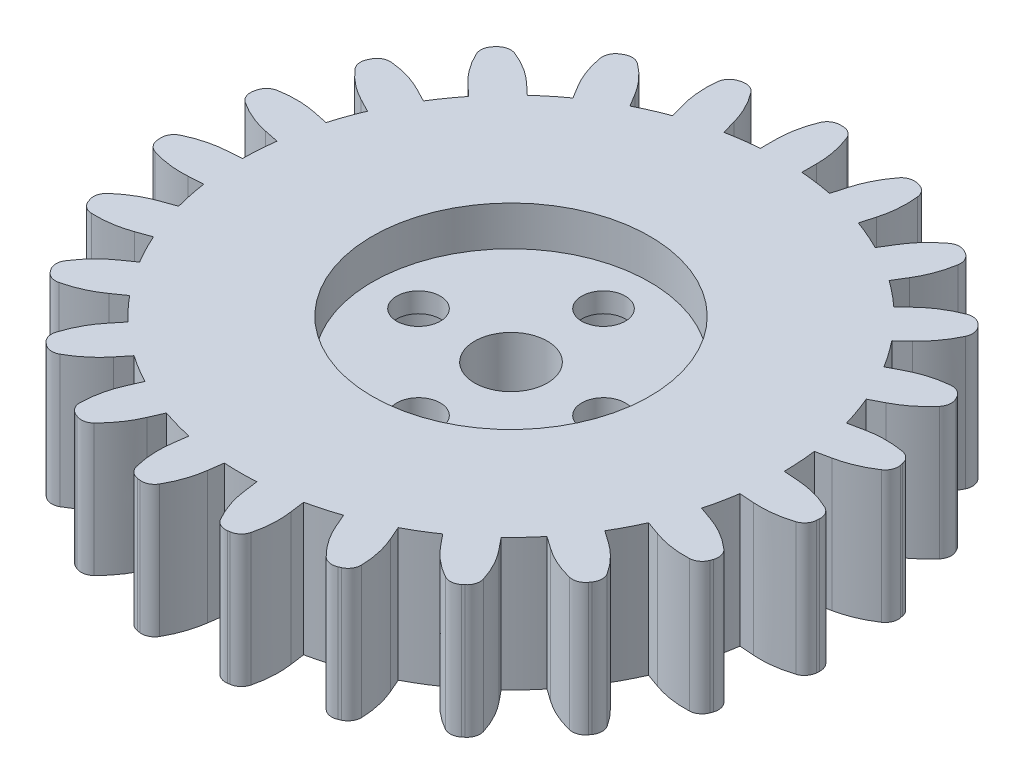
SolidWorks part; units mm, degrees
ref_plane "Plan de face" through (0, 0, 0) normal (0, 0, 1) x (1, 0, 0)
ref_plane "Plan de dessus" through (0, 0, 0) normal (0, 1, 0) x (1, 0, 0)
ref_plane "Plan de droite" through (0, 0, 0) normal (1, 0, 0) x (0, 0, -1)
sketch "Esquisse1" plane through (0, 0, 0) normal (0, 1, 0) x (1, 0, 0)
  line L0 (0, 0) -> (5.1978, 24.4537) construction
  line L1 (0, 0) -> (-5.1978, 24.4537) construction
  line L2 (0, 0) -> (0, 25) construction
  line L3 (-1.57, 20.4398) -> (1.57, 20.4398) construction
  line L5 (-0.74, 24.989) -> (0, 0) construction
  line L6 (0, 0) -> (-4.2622, 20.052)
  line L7 (-1.57, 20.4398) -> (1.57, 20.4398) construction
  line L8 (-1.57, 20.4398) -> (-1.57, 21.5579)
  line L9 (-1.57, 21.5579) -> (1.57, 21.5579) construction
  line L10 (1.57, 20.4398) -> (1.57, 21.5579)
  line L11 (-1.44, 22.9549) -> (0, 0) construction
  line L12 (0, 0) -> (4.2622, 20.052)
  line L13 (-0.74, 24.989) -> (0.74, 24.989) construction
  line L14 (-1.44, 22.9549) -> (1.44, 22.9549) construction
  circle A0 centre (0, 0) radius 20.5 construction
  circle A1 centre (0, 0) radius 25 construction
  circle A2 centre (0, 0) radius 23 construction
  circle A3 centre (0, 0) radius 21.615 construction
  arc A4 (-1.57, 20.4398) -> (-4.2622, 20.052) centre (0, 0) ccw
  arc A5 (1.57, 20.4398) -> (4.2622, 20.052) centre (0, 0) cw
  arc A6 (-0.74, 24.989) -> (0.74, 24.989) centre (0, 0) cw
  spline S0 degree 2 poles (-0.74, 24.989) (-1.5686, 23.3625) (-1.57, 21.5579) knots 0 0 0 1 1 1
  spline S1 degree 2 poles (0.74, 24.989) (1.5686, 23.3625) (1.57, 21.5579) knots 0 0 0 1 1 1
  dimension "D1" = 41
  dimension "D2" = 43.23
  dimension "D3" = 46
  dimension "D4" = 50
  dimension "D5" = 24
  dimension "D6" = 12
  dimension "D7" = 3.14
  dimension "D8" = 1.48
  dimension "D9" = 2.88
extrude "Boss.-Extru.2" add sketch "Esquisse1" along normal blind 10 contours S1 A6 S0 L8 A4 L6 L12 A5 L10
fillet "Congé1" radius 1 2 edges at (0.74, 5, -24.989) (-0.74, 5, -24.989)
pattern_circular "Répétition circulaire1" count 23 over 360 about axis through (0, 10, 0) along (0, -1, 0) of "Boss.-Extru.2", "Congé1"
sketch "Esquisse2" plane through (0, 10, 0) normal (0, 1, 0) x (1, 0, 0)
  circle A0 centre (0, 0) radius 10.5
  dimension "D1" = 21
extrude "Enlèv. mat.-Extru.1" cut sketch "Esquisse2" against normal blind 3
sketch "Esquisse3" plane through (0, 7, 0) normal (0, 1, 0) x (1, 0, 0)
  line L0 (0, 7) -> (0, 0) construction
  circle A0 centre (0, 0) radius 2.75
  circle A1 centre (0, 7) radius 1.65
  circle A5 centre (7, 0) radius 1.65
  circle A6 centre (0, -7) radius 1.65
  circle A7 centre (-7, 0) radius 1.65
  point P14 (0, 0)
  dimension "D1" = 5.5
  dimension "D2" = 3.3
  dimension "D3" = 7
  dimension "D4" = 4
extrude "Enlèv. mat.-Extru.2" cut sketch "Esquisse3" against normal through all
sketch "Esquisse4" plane through (0, 0, 0) normal (0, -1, 0) x (1, 0, 0)
  circle A0 centre (0, 7) radius 2.75
  circle A4 centre (7, 0) radius 2.75
  circle A5 centre (0, -7) radius 2.75
  circle A6 centre (-7, 0) radius 2.75
  point P10 (0, 7)
  point P13 (0, 0)
  dimension "D1" = 5.5
  dimension "D2" = 4
extrude "Enlèv. mat.-Extru.3" cut sketch "Esquisse4" against normal offset from surface (5.5 mm away) 1.5 up to face at (0, 7, 2.75)
